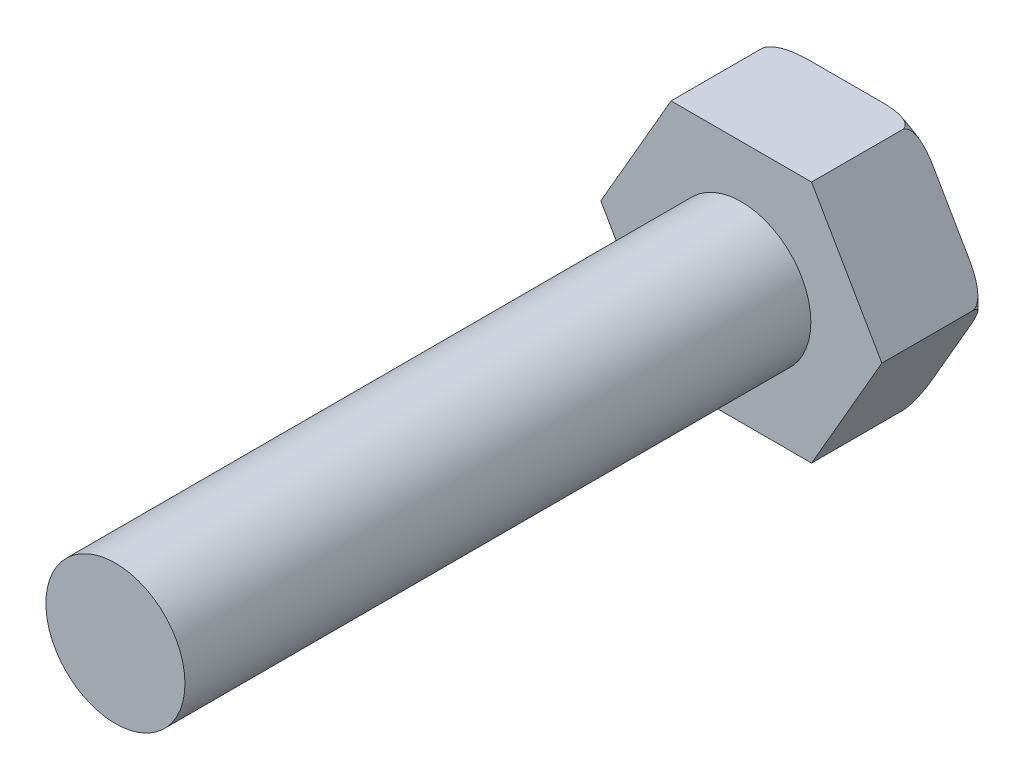
SolidWorks part; units mm, degrees
ref_plane "Front Plane" through (0, 0, 0) normal (0, 0, 1) x (1, 0, 0)
ref_plane "Top Plane" through (0, 0, 0) normal (0, 1, 0) x (1, 0, 0)
ref_plane "Right Plane" through (0, 0, 0) normal (1, 0, 0) x (0, 0, -1)
sketch "Sketch1" plane through (0, 0, 0) normal (0, 0, 1) x (1, 0, 0)
  line L1 (-20.2073, 0) -> (-10.1036, -17.5)
  line L2 (-10.1036, -17.5) -> (10.1036, -17.5)
  line L3 (10.1036, -17.5) -> (20.2073, 0)
  line L4 (20.2073, 0) -> (10.1036, 17.5)
  line L5 (10.1036, 17.5) -> (-10.1036, 17.5)
  line L6 (-10.1036, 17.5) -> (-20.2073, 0)
  circle A0 centre (0, 0) radius 17.5 construction
  point P1 (0, 0)
  dimension "D1" = 35
extrude "Boss-Extrude1" add sketch "Sketch1" along normal blind 15
sketch "Sketch2" plane through (0, 0, 15) normal (0, 0, 1) x (1, 0, 0)
  circle A0 centre (0, 0) radius 10
  dimension "D1" = 20
extrude "Boss-Extrude2" add sketch "Sketch2" along normal blind 90
sketch "Sketch3" plane through (0, 0, 0) normal (0, 1, 0) x (1, 0, 0)
  line L0 (20.2073, 0) -> (10.1036, 0) construction
  line L1 (20.2073, -15) -> (20.2073, 0) construction
  line L2 (18.2073, 0) -> (20.2073, 0)
  line L3 (20.2073, 0) -> (20.2073, -2)
  arc A0 (18.2073, 0) -> (20.2073, -2) centre (18.2073, -2) cw
  dimension "D1" = 2
revolve "Cut-Revolve2" cut sketch "Sketch3" angle 360 about axis through (0, 0, 105) along (0, 0, -1)
